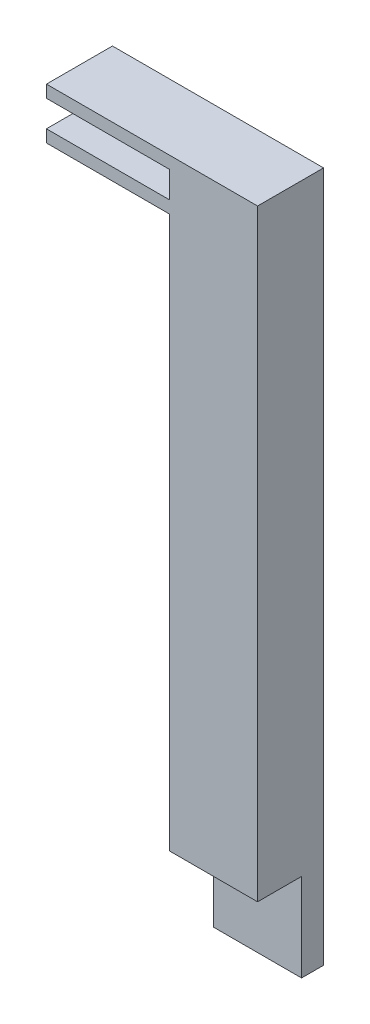
SolidWorks part; units mm, degrees
ref_plane "Front Plane" through (0, 0, 0) normal (0, 0, 1) x (1, 0, 0)
ref_plane "Top Plane" through (0, 0, 0) normal (0, 1, 0) x (1, 0, 0)
ref_plane "Right Plane" through (0, 0, 0) normal (1, 0, 0) x (0, 0, -1)
sketch "Sketch1" plane through (0, 0, 0) normal (0, 0, 1) x (1, 0, 0)
  line L1 (-31.75, -76.2) -> (31.75, -76.2)
  line L2 (-31.75, -76.2) -> (-31.75, 76.2)
  line L3 (-31.75, 76.2) -> (31.75, 76.2)
  line L4 (31.75, -76.2) -> (31.75, 76.2)
  line L5 (-31.75, -76.2) -> (31.75, 76.2) construction
  line L6 (-31.75, 76.2) -> (31.75, -76.2) construction
  line L7 (-31.75, -76.2) -> (-19.05, -76.2)
  line L8 (-31.75, -76.2) -> (-31.75, -63.5)
  line L9 (-31.75, -63.5) -> (-19.05, -63.5)
  line L10 (-19.05, -76.2) -> (-19.05, -63.5)
  line L11 (31.75, -76.2) -> (19.05, -76.2)
  line L12 (31.75, -76.2) -> (31.75, -63.5)
  line L13 (31.75, -63.5) -> (19.05, -63.5)
  line L14 (19.05, -76.2) -> (19.05, -63.5)
  line L15 (31.75, 76.2) -> (19.05, 76.2)
  line L16 (31.75, 76.2) -> (31.75, 63.5)
  line L17 (31.75, 63.5) -> (19.05, 63.5)
  line L18 (19.05, 76.2) -> (19.05, 63.5)
  line L19 (-31.75, 76.2) -> (-19.05, 76.2)
  line L20 (-31.75, 76.2) -> (-31.75, 63.5)
  line L21 (-31.75, 63.5) -> (-19.05, 63.5)
  line L22 (-19.05, 76.2) -> (-19.05, 63.5)
  circle A0 centre (-19.05, 63.5) radius 3.175
  circle A1 centre (19.05, 63.5) radius 3.175
  circle A2 centre (-19.05, -63.5) radius 3.175
  circle A3 centre (19.05, -63.5) radius 3.175
  point P0 (0, 0)
extrude "Boss-Extrude1" add sketch "Sketch1" along normal blind 25.4 contours A3 L13 L4 L17 A1 L18 L3 L22 A0 L21 L2 L9 A2 L10 L1 L14 | A0 L22 L3 L2 L21 | A1 L17 L4 L3 L18 | A2 L9 L2 L1 L10 | A3 L14 L1 L4 L13
sketch "Sketch2" plane through (0, 0, 25.4) normal (0, 0, 1) x (1, 0, 0)
  line L0 (31.75, -76.2) -> (31.75, 76.2) construction
  line L1 (-31.75, 76.2) -> (31.75, 76.2)
  line L2 (-31.75, 76.2) -> (-31.75, 50.8)
  line L3 (-31.75, 50.8) -> (31.75, 50.8)
  line L4 (31.75, 76.2) -> (31.75, 50.8)
  line L5 (-31.75, -76.2) -> (-31.75, 76.2) construction
  line L6 (31.75, -76.2) -> (-31.75, -76.2)
  line L7 (31.75, -76.2) -> (31.75, -50.8)
  line L8 (31.75, -50.8) -> (-31.75, -50.8)
  line L9 (-31.75, -76.2) -> (-31.75, -50.8)
extrude "Cut-Extrude1" cut sketch "Sketch2" against normal blind 19.05
sketch "Sketch3" plane through (0, 0, 25.4) normal (0, 0, 1) x (1, 0, 0)
  circle A0 centre (0, 0) radius 15.875
extrude "Cut-Extrude4" cut sketch "Sketch3" against normal through all
sketch "Sketch5" plane through (0, 0, 25.4) normal (0, 0, 1) x (1, 0, 0)
  circle A0 centre (0, 0) radius 15.875
  circle A1 centre (0, 0) radius 22.225
  dimension "D1" = 6.35
extrude "Cut-Extrude6" cut sketch "Sketch5" against normal blind 19.05
sketch "Sketch6" plane through (0, 0, 25.4) normal (0, 0, 1) x (1, 0, 0)
  line L0 (31.75, -50.8) -> (-31.75, -50.8) construction
  line L1 (-12.7, 0) -> (12.7, 0)
  circle A0 centre (0, -50.8) radius 12.7
  circle A1 centre (0, 50.8) radius 12.7
  point P9 (0, 0)
extrude "Cut-Extrude7" cut sketch "Sketch6" against normal blind 3.175 contours A1 | A0
sketch "Sketch7" plane through (-31.75, 0, 0) normal (-1, 0, 0) x (0, 0, 1)
  line L26 (6.35, -50.8) -> (25.4, -50.8) construction
  line L27 (0, 123.19) -> (19.05, 123.19)
  line L28 (6.35, -50.8) -> (19.05, -50.8)
  line L32 (25.4, 50.8) -> (6.35, 50.8)
  line L33 (6.35, 50.8) -> (6.35, 76.2)
  line L34 (6.35, 76.2) -> (0, 76.2)
  line L35 (0, 76.2) -> (0, -76.2)
  line L36 (0, -76.2) -> (6.35, -76.2)
  line L37 (6.35, -76.2) -> (6.35, -50.8)
  line L38 (6.35, -50.8) -> (25.4, -50.8)
  line L39 (25.4, -50.8) -> (25.4, 50.8)
  line L43 (0, 123.19) -> (0, -76.2)
  line L44 (0, -76.2) -> (6.35, -76.2)
  line L45 (6.35, -76.2) -> (6.35, -50.8)
  line L47 (19.05, -50.8) -> (19.05, 123.19)
  dimension "D2" = 19.05
  dimension "D3" = 173.99
  dimension "D1" = 0
extrude "Boss-Extrude2" add sketch "Sketch7" along normal blind 25.4 separate body
sketch "Sketch9" plane through (-57.15, 0, 0) normal (-1, 0, 0) x (0, 0, 1)
  line L0 (0, 123.19) -> (19.05, 123.19)
  line L1 (19.05, 123.19) -> (0, 123.19) construction
  line L2 (19.05, 123.19) -> (19.05, 119.634)
  line L3 (19.05, -50.8) -> (19.05, 123.19) construction
  line L4 (19.05, 119.634) -> (0, 119.634)
  line L5 (0, 123.19) -> (0, -76.2) construction
  line L6 (0, 119.634) -> (0, 123.19)
  line L7 (0, 112.014) -> (19.05, 112.014)
  line L8 (19.05, 112.014) -> (19.05, 108.458)
  line L9 (19.05, 108.458) -> (0, 108.458)
  line L10 (0, 108.458) -> (0, 112.014)
  dimension "D1" = 3.556
  dimension "D2" = 3.556
  dimension "D3" = 7.62
extrude "Boss-Extrude4" add sketch "Sketch9" along normal blind 35.56
delete or keep bodies "Body-Delete/Keep 1" type keep bodies bodies 111
